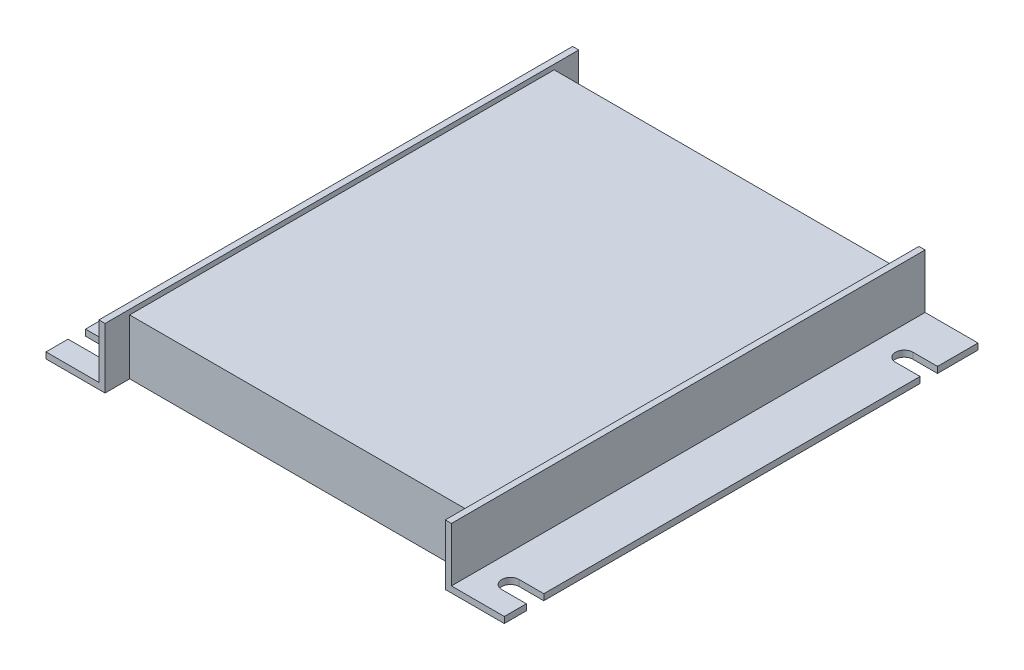
SolidWorks part; units mm, degrees
ref_plane "Front Plane" through (0, 0, 0) normal (0, 0, 1) x (1, 0, 0)
ref_plane "Top Plane" through (0, 0, 0) normal (0, 1, 0) x (1, 0, 0)
ref_plane "Right Plane" through (0, 0, 0) normal (1, 0, 0) x (0, 0, -1)
sketch "Sketch2" plane through (0, 0, 0) normal (0, 1, 0) x (1, 0, 0)
  line L1 (0, 0) -> (118.2687, 0)
  line L2 (0, 0) -> (0, 122.2375)
  line L3 (0, 122.2375) -> (118.2687, 122.2375)
  line L4 (118.2687, 0) -> (118.2687, 122.2375)
  dimension "D1" = 118.2687
  dimension "D2" = 122.2375
extrude "Boss-Extrude1" add sketch "Sketch2" along normal blind 1.5875
sketch "Sketch3" plane through (0, 1.5875, 0) normal (0, 1, 0) x (1, 0, 0)
  line L0 (118.2687, 0) -> (118.2687, 122.2375) construction
  line L1 (15.24, 115.8875) -> (103.0287, 115.8875)
  line L2 (15.24, 115.8875) -> (15.24, 6.35)
  line L3 (15.24, 6.35) -> (103.0288, 6.35)
  line L4 (103.0287, 115.8875) -> (103.0288, 6.35)
  line L5 (0, 122.2375) -> (0, 0) construction
  line L9 (118.2687, 122.2375) -> (0, 122.2375) construction
  line L10 (0, 0) -> (118.2687, 0) construction
  dimension "D1" = 15.24
  dimension "D2" = 15.24
  dimension "D3" = 6.35
  dimension "D4" = 6.35
extrude "Boss-Extrude2" add sketch "Sketch3" along normal blind 12.7
sketch "Sketch4" plane through (0, 1.5875, 0) normal (0, 1, 0) x (1, 0, 0)
  line L0 (15.24, 122.2375) -> (15.24, 0)
  line L1 (118.2687, 122.2375) -> (0, 122.2375) construction
  line L2 (0, 0) -> (118.2687, 0) construction
  line L3 (15.24, 0) -> (13.6525, 0)
  line L4 (13.6525, 0) -> (13.6525, 122.2375)
  line L5 (13.6525, 122.2375) -> (15.24, 122.2375)
  line L6 (103.0288, 0) -> (103.0288, 122.2375)
  line L7 (103.0288, 122.2375) -> (104.6163, 122.2375)
  line L8 (104.6163, 122.2375) -> (104.6163, 0)
  line L9 (104.6163, 0) -> (103.0288, 0)
  line L10 (103.0288, 6.35) -> (103.0288, 115.8875) construction
  dimension "D1" = 1.5875
  dimension "D2" = 1.5875
extrude "Boss-Extrude3" add sketch "Sketch4" along normal blind 13.97
sketch "Sketch5" plane through (0, 1.5875, 0) normal (0, 1, 0) x (1, 0, 0)
  line L0 (-8.7312, 109.5375) -> (8.7312, 109.5375) construction
  line L1 (0, 122.2375) -> (0, 0) construction
  line L2 (-8.7312, 111.7854) -> (8.7312, 111.7854)
  line L3 (-8.7312, 107.2896) -> (8.7312, 107.2896)
  line L4 (13.6525, 122.2375) -> (0, 122.2375) construction
  line L5 (111.9187, 109.5375) -> (129.3812, 109.5375) construction
  line L6 (111.9187, 111.7854) -> (129.3812, 111.7854)
  line L7 (111.9187, 107.2896) -> (129.3812, 107.2896)
  line L8 (111.9188, 7.9375) -> (129.3813, 7.9375) construction
  line L9 (111.9188, 10.1854) -> (129.3813, 10.1854)
  line L10 (111.9188, 5.6896) -> (129.3813, 5.6896)
  line L11 (-8.7312, 7.9375) -> (8.7313, 7.9375) construction
  line L12 (-8.7312, 10.1854) -> (8.7313, 10.1854)
  line L13 (-8.7312, 5.6896) -> (8.7313, 5.6896)
  line L14 (103.0288, 122.2375) -> (103.0288, 0) construction
  line L15 (15.24, 115.8875) -> (103.0288, 115.8875)
  line L16 (15.24, 115.8875) -> (15.24, 125.4392)
  line L17 (15.24, 125.4392) -> (103.0288, 125.4392)
  line L18 (103.0288, 115.8875) -> (103.0288, 125.4392)
  line L19 (103.0288, 6.35) -> (103.0288, 0) construction
  line L20 (15.24, 6.35) -> (103.0288, 6.35)
  line L21 (15.24, 6.35) -> (15.24, -3.2309)
  line L22 (15.24, -3.2309) -> (103.0288, -3.2309)
  line L23 (103.0288, 6.35) -> (103.0288, -3.2309)
  arc A0 (-8.7312, 111.7854) -> (-8.7312, 107.2896) centre (-8.7312, 109.5375) ccw
  arc A1 (8.7312, 107.2896) -> (8.7312, 111.7854) centre (8.7312, 109.5375) ccw
  arc A2 (111.9187, 111.7854) -> (111.9187, 107.2896) centre (111.9187, 109.5375) ccw
  arc A3 (129.3812, 107.2896) -> (129.3812, 111.7854) centre (129.3812, 109.5375) ccw
  arc A4 (111.9188, 10.1854) -> (111.9188, 5.6896) centre (111.9188, 7.9375) ccw
  arc A5 (129.3813, 5.6896) -> (129.3813, 10.1854) centre (129.3813, 7.9375) ccw
  arc A6 (-8.7312, 10.1854) -> (-8.7312, 5.6896) centre (-8.7312, 7.9375) ccw
  arc A7 (8.7313, 5.6896) -> (8.7313, 10.1854) centre (8.7313, 7.9375) ccw
  point P4 (0, 109.5375)
  point P15 (120.65, 109.5375)
  point P22 (120.65, 7.9375)
  point P29 (0, 7.9375)
  dimension "D1" = 2.2479
  dimension "D2" = 12.7
  dimension "D5" = 103.1875
  dimension "D6" = 101.6
  dimension "D3" = 2
  dimension "D4" = 2
extrude "Cut-Extrude1" cut sketch "Sketch5" against normal through all
